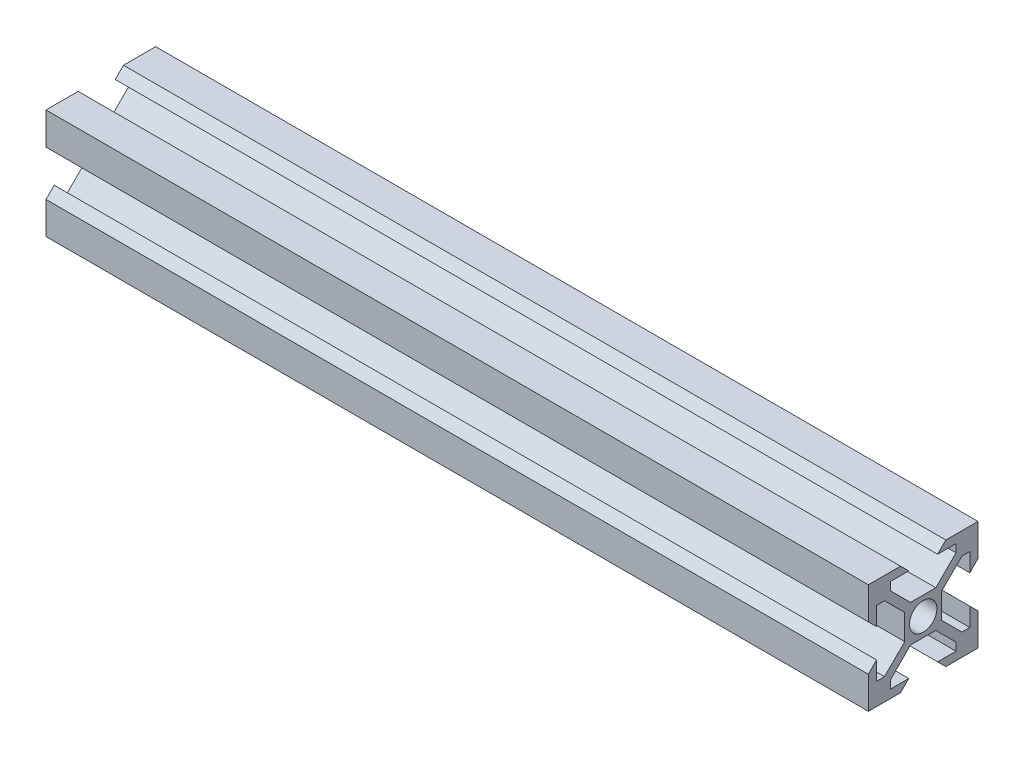
SolidWorks part; units mm, degrees
ref_plane "Front Plane" through (0, 0, 0) normal (0, 0, 1) x (1, 0, 0)
ref_plane "Top Plane" through (0, 0, 0) normal (0, 1, 0) x (1, 0, 0)
ref_plane "Right Plane" through (0, 0, 0) normal (1, 0, 0) x (0, 0, -1)
sketch "Sketch1" plane through (0, 0, 0) normal (1, 0, 0) x (0, 0, -1)
  line L0 (0, 0) -> (10, 0) construction
  line L2 (10, 10) -> (-10, 10) construction
  line L3 (-10, 10) -> (-10, -10) construction
  line L4 (-10, -10) -> (10, -10) construction
  line L6 (10, -10) -> (10, 10) construction
  line L7 (-10, -10) -> (10, 10) construction
  line L8 (10, 8.9393) -> (-8.9393, -10)
  line L9 (-10, -8.9393) -> (8.9393, 10)
  line L10 (0, 0) -> (3.365, 0) construction
  line L11 (3.365, -3.365) -> (3.365, 3.365)
  line L12 (3.365, 3.365) -> (-3.365, 3.365)
  line L13 (-3.365, 3.365) -> (-3.365, -3.365)
  line L14 (-3.365, -3.365) -> (3.365, -3.365)
  line L15 (-10, -10) -> (-10, -2.63)
  line L16 (-10, -2.63) -> (-8.5, -2.63)
  line L17 (-8.5, -2.63) -> (-8.5, -5.995)
  line L18 (-8.5, -5.995) -> (-7.0557, -5.995)
  line L19 (-8.5, -2.63) -> (-10, -4.13)
  line L20 (-10, -10) -> (-2.63, -10)
  line L21 (-2.63, -10) -> (-2.63, -8.5)
  line L22 (-2.63, -8.5) -> (-5.995, -8.5)
  line L23 (-2.63, -8.5) -> (-4.13, -10)
  line L24 (-5.995, -8.5) -> (-5.995, -7.0557)
  line L25 (-10, 10) -> (-2.63, 10)
  line L26 (-2.63, 8.5) -> (-5.995, 8.5)
  line L27 (-5.995, 8.5) -> (-5.995, 7.0557)
  line L28 (-10, 10) -> (-10, 2.63)
  line L29 (-10, 2.63) -> (-8.5, 2.63)
  line L30 (-8.5, 2.63) -> (-8.5, 5.995)
  line L31 (-8.5, 2.63) -> (-10, 4.13)
  line L32 (-8.5, 5.995) -> (-7.0557, 5.995)
  line L33 (10, 10) -> (-10, 10) construction
  line L34 (-10, 10) -> (-10, -10) construction
  line L35 (-2.63, 10) -> (-2.63, 8.5)
  line L36 (-2.63, 8.5) -> (-4.13, 10)
  line L37 (10, 10) -> (10, 2.63)
  line L38 (8.5, 2.63) -> (8.5, 5.995)
  line L39 (8.5, 5.995) -> (7.0557, 5.995)
  line L40 (10, 10) -> (2.63, 10)
  line L41 (2.63, 10) -> (2.63, 8.5)
  line L42 (2.63, 8.5) -> (5.995, 8.5)
  line L43 (2.63, 8.5) -> (4.13, 10)
  line L44 (5.995, 8.5) -> (5.995, 7.0557)
  line L45 (10, -10) -> (10, 10) construction
  line L46 (10, 10) -> (-10, 10) construction
  line L47 (10, 2.63) -> (8.5, 2.63)
  line L48 (8.5, 2.63) -> (10, 4.13)
  line L49 (10, -10) -> (2.63, -10)
  line L50 (2.63, -8.5) -> (5.995, -8.5)
  line L51 (5.995, -8.5) -> (5.995, -7.0557)
  line L52 (10, -10) -> (10, -2.63)
  line L53 (10, -2.63) -> (8.5, -2.63)
  line L54 (8.5, -2.63) -> (8.5, -5.995)
  line L55 (8.5, -2.63) -> (10, -4.13)
  line L56 (8.5, -5.995) -> (7.0557, -5.995)
  line L57 (-10, -10) -> (10, -10) construction
  line L58 (10, -10) -> (10, 10) construction
  line L59 (2.63, -10) -> (2.63, -8.5)
  line L60 (2.63, -8.5) -> (4.13, -10)
  line L61 (8.9393, -10) -> (-10, 8.9393)
  line L62 (-10, -8.9393) -> (8.9393, 10)
  line L63 (-8.9393, 10) -> (10, -8.9393)
  circle A0 centre (0, 0) radius 2.5
  point P28 (0, 0)
  dimension "D1" = 5
  dimension "D2" = 10
  dimension "D3" = 10
  dimension "D4" = 20
  dimension "D5" = 0.75
  dimension "D6" = 0.75
  dimension "D7" = 3.365
  dimension "D8" = 6.73
  dimension "D9" = 7.37
  dimension "D10" = 1.5
  dimension "D11" = 3.365
  dimension "D12" = 45
  dimension "D13" = 4
  dimension "D14" = 4
extrude "Boss-Extrude1" add sketch "Sketch1" along normal blind 150 contours L49 L61 L51 L50 L60 | L56 L63 L52 L55 L54 | L63 L11 L14 L61 L49 L52 | A0 L61 L14 L11 L63 | A0 L63 L11 L8 | A0 L8 L11 L12 L9 | A0 L9 L12 L63 | A0 L63 L12 L13 L61 | A0 L61 L13 L9 | A0 L9 L13 L14 L8 | A0 L8 L14 L61 | L38 L48 L37 L8 L39 | L37 L40 L9 L12 L11 L8 | L42 L44 L9 L40 L43 | L25 L63 L27 L26 L36 | L63 L25 L28 L61 L13 L12 | L32 L61 L28 L31 L30 | L17 L19 L15 L9 L18 | L15 L20 L8 L14 L13 L9 | L22 L24 L8 L20 L23
